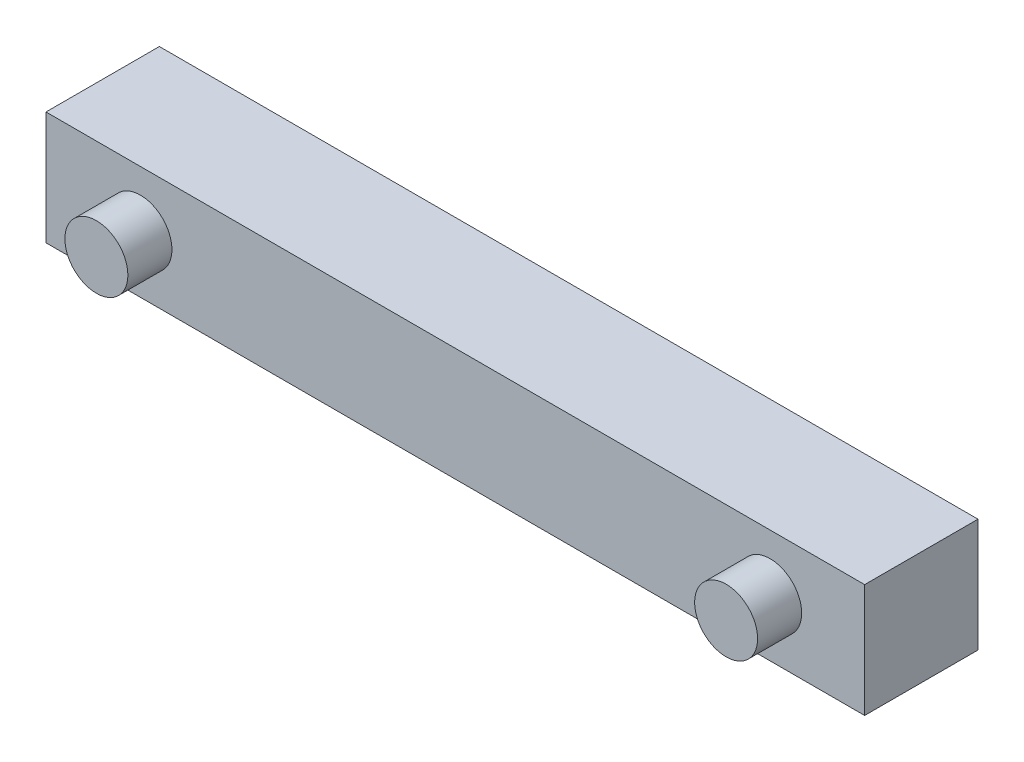
SolidWorks part; units mm, degrees
ref_plane "Front Plane" through (0, 0, 0) normal (0, 0, 1) x (1, 0, 0)
ref_plane "Top Plane" through (0, 0, 0) normal (0, 1, 0) x (1, 0, 0)
ref_plane "Right Plane" through (0, 0, 0) normal (1, 0, 0) x (0, 0, -1)
sketch "Sketch1" plane through (0, 0, 0) normal (0, 0, 1) x (1, 0, 0)
  line L1 (0, 0) -> (65, 0)
  line L2 (0, 0) -> (0, 9)
  line L3 (0, 9) -> (65, 9)
  line L4 (65, 0) -> (65, 9)
  dimension "D1" = 65
  dimension "D2" = 9
extrude "Boss-Extrude1" add sketch "Sketch1" along normal blind 9
sketch "Sketch2" plane through (0, 0, 9) normal (0, 0, 1) x (1, 0, 0)
  line L0 (0, 9) -> (0, 0) construction
  line L1 (65, 0) -> (65, 9) construction
  circle A0 centre (7.5, 4.5301) radius 2.5
  circle A1 centre (57.5, 4.5301) radius 2.5
  point P2 (0, 4.5)
  dimension "D2" = 5
  dimension "D3" = 5
  dimension "D1" = 7.5
  dimension "D4" = 50
  dimension "D5" = 7.5
extrude "Boss-Extrude2" add sketch "Sketch2" along normal blind 3.5
